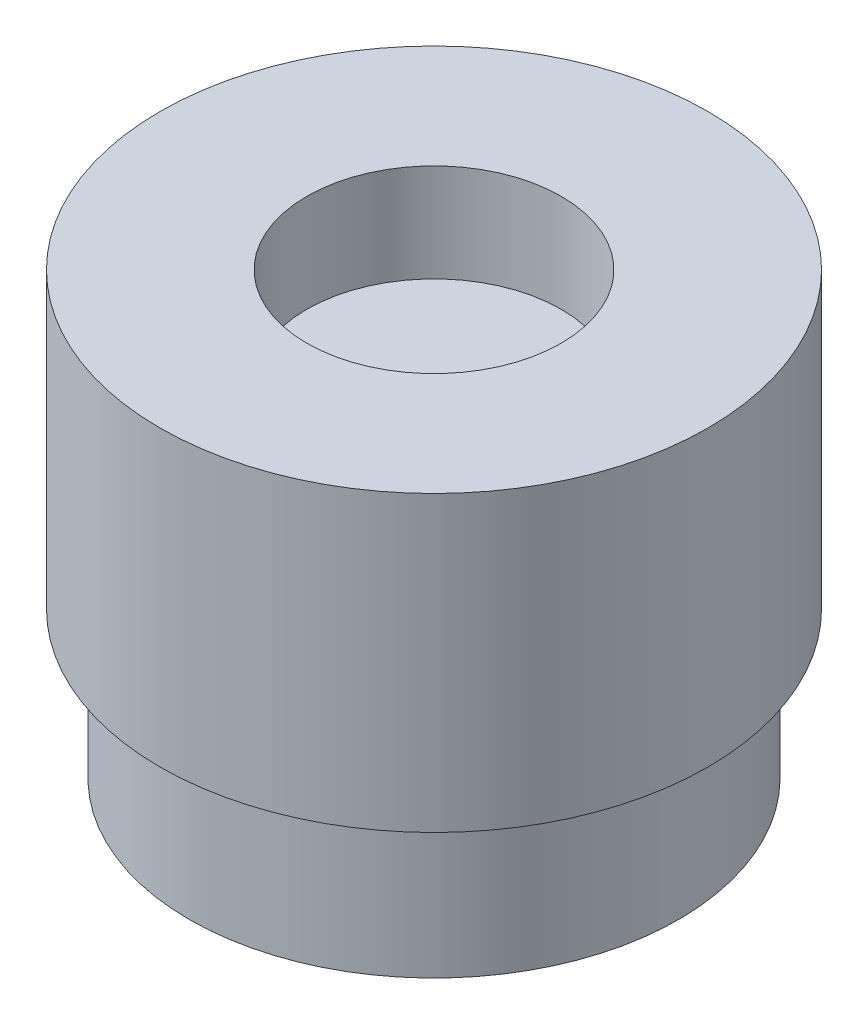
SolidWorks part; units mm, degrees
material "PET"
ref_plane "Front Plane" through (0, 0, 0) normal (0, 0, 1) x (1, 0, 0)
ref_plane "Top Plane" through (0, 0, 0) normal (0, 1, 0) x (1, 0, 0)
ref_plane "Right Plane" through (0, 0, 0) normal (1, 0, 0) x (0, 0, -1)
sketch "Sketch1" plane through (0, 0, 0) normal (0, 1, 0) x (1, 0, 0)
  circle A0 centre (0, 0) radius 1.5
  circle A1 centre (0, 0) radius 5
  dimension "D1" = 3
  dimension "D2" = 10
extrude "Boss-Extrude1" add sketch "Sketch1" along normal blind 3
sketch "Sketch3" plane through (0, 3, 0) normal (0, 1, 0) x (1, 0, 0)
  circle A0 centre (0, 0) radius 3.75
  circle A2 centre (0, 0) radius 4.5
  circle A3 centre (0, 0) radius 5
  circle A4 centre (0, 0) radius 5
  dimension "D1" = 7.5
  dimension "D3" = 9
  dimension "D2" = 0
extrude "Boss-Extrude2" add sketch "Sketch3" along normal blind 2.5 contours A2 A0
sketch "Sketch4" plane through (0, 5.5, 0) normal (0, 1, 0) x (1, 0, 0)
  line L0 (0, 0) -> (0, 5) construction
  line L2 (-1, 3.6142) -> (1, 3.6142)
  line L3 (-1, 3.6142) -> (-1, 5)
  line L4 (-1, 5) -> (1, 5)
  line L5 (1, 3.6142) -> (1, 5)
  line L6 (-1, 3.6142) -> (1, 5) construction
  line L7 (-1, 5) -> (1, 3.6142) construction
  circle A0 centre (0, 0) radius 5 construction
  circle A1 centre (0, 0) radius 3.75 construction
  point P6 (0, 4.3071)
  dimension "D1" = 5
  dimension "D2" = 2
extrude "Cut-Extrude1" cut sketch "Sketch4" against normal up to surface (2.5 mm away) up to face at (0, 3, 4.5)
sketch "Sketch5" plane through (0, 3, 0) normal (0, 1, 0) x (1, 0, 0)
  line L0 (0, 0) -> (0, 5) construction
  line L1 (1, 3.6142) -> (1, 4.3875) construction
  line L2 (-0.95, 3.75) -> (0.95, 3.75)
  line L3 (-0.95, 3.75) -> (-0.95, 5)
  line L4 (-0.95, 5) -> (0.95, 5)
  line L5 (0.95, 3.75) -> (0.95, 5)
  line L6 (-0.95, 3.75) -> (0.95, 5) construction
  line L7 (-0.95, 5) -> (0.95, 3.75) construction
  circle A0 centre (0, 0) radius 4.6
  arc A1 (-1, 4.3875) -> (1, 4.3875) centre (0, 0) ccw construction
  circle A2 centre (0, 0) radius 5.6
  circle A3 centre (0, 0) radius 5 construction
  circle A4 centre (0, 0) radius 3.75
  point P8 (0, 4.375)
  circle M6 centre (0, 0) radius 5
  dimension "D1" = 0.1
  dimension "D4" = 7.5
  dimension "D3" = 0.05
  dimension "D2" = 1
extrude "Boss-Extrude3" add sketch "Sketch5" along normal blind 3 separate body contours A2 L5 L3 L4 M6 | A0 L3 L5 M6 | A0 L5 L3 M6 | L5 A0 L3 L2 | L4 L3 M6 | L5 L4 M6
sketch "Sketch6" plane through (0, 6, 0) normal (0, 1, 0) x (1, 0, 0)
  circle A3 centre (0, 0) radius 5.6
  circle A4 centre (0, 0) radius 5.6
  dimension "D1" = 0
extrude "Boss-Extrude4" add sketch "Sketch6" along normal blind 1
sketch "Sketch7" plane through (0, 7, 0) normal (0, 1, 0) x (1, 0, 0)
  circle A0 centre (0, 0) radius 2.6
  circle A3 centre (0, 0) radius 5.6
  circle A4 centre (0, 0) radius 5.6
  dimension "D1" = 5.2
  dimension "D2" = 0
extrude "Boss-Extrude5" add sketch "Sketch7" along normal blind 2
other "Save Bodies1"
